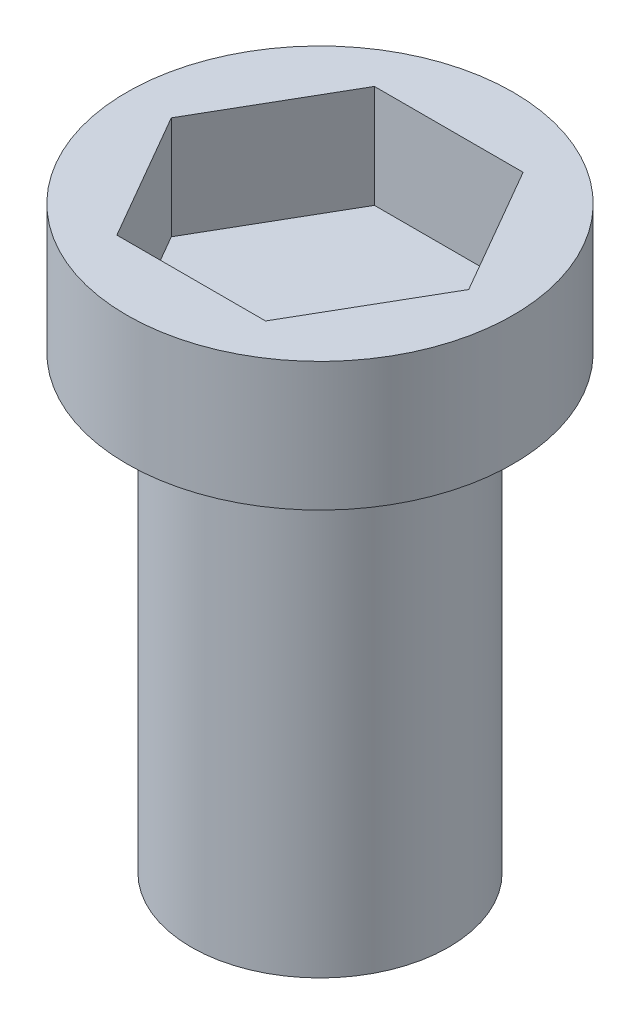
SolidWorks part; units mm, degrees
ref_plane "Front Plane" through (0, 0, 0) normal (0, 0, 1) x (1, 0, 0)
ref_plane "Top Plane" through (0, 0, 0) normal (0, 1, 0) x (1, 0, 0)
ref_plane "Right Plane" through (0, 0, 0) normal (1, 0, 0) x (0, 0, -1)
sketch "Sketch2" plane through (0, 0, 0) normal (0, 1, 0) x (1, 0, 0)
  line L1 (5.7735, 10) -> (-5.7735, 10)
  line L2 (-5.7735, 10) -> (-11.547, 0)
  line L3 (-11.547, 0) -> (-5.7735, -10)
  line L4 (-5.7735, -10) -> (5.7735, -10)
  line L5 (5.7735, -10) -> (11.547, 0)
  line L6 (11.547, 0) -> (5.7735, 10)
  circle A0 centre (0, 0) radius 15
  circle A1 centre (0, 0) radius 10 construction
  dimension "D1" = 30
  dimension "D2" = 20
extrude "Boss-Extrude1" add sketch "Sketch2" along normal blind 10
sketch "Sketch4" plane through (0, 0, 0) normal (0, -1, 0) x (1, 0, 0)
  circle A0 centre (0, 0) radius 15
  dimension "D1" = 30
extrude "Boss-Extrude2" add sketch "Sketch4" against normal blind 2
sketch "Sketch5" plane through (0, 0, 0) normal (0, -1, 0) x (1, 0, 0)
  circle A0 centre (0, 0) radius 10
  dimension "D1" = 20
extrude "Boss-Extrude3" add sketch "Sketch5" along normal blind 35
